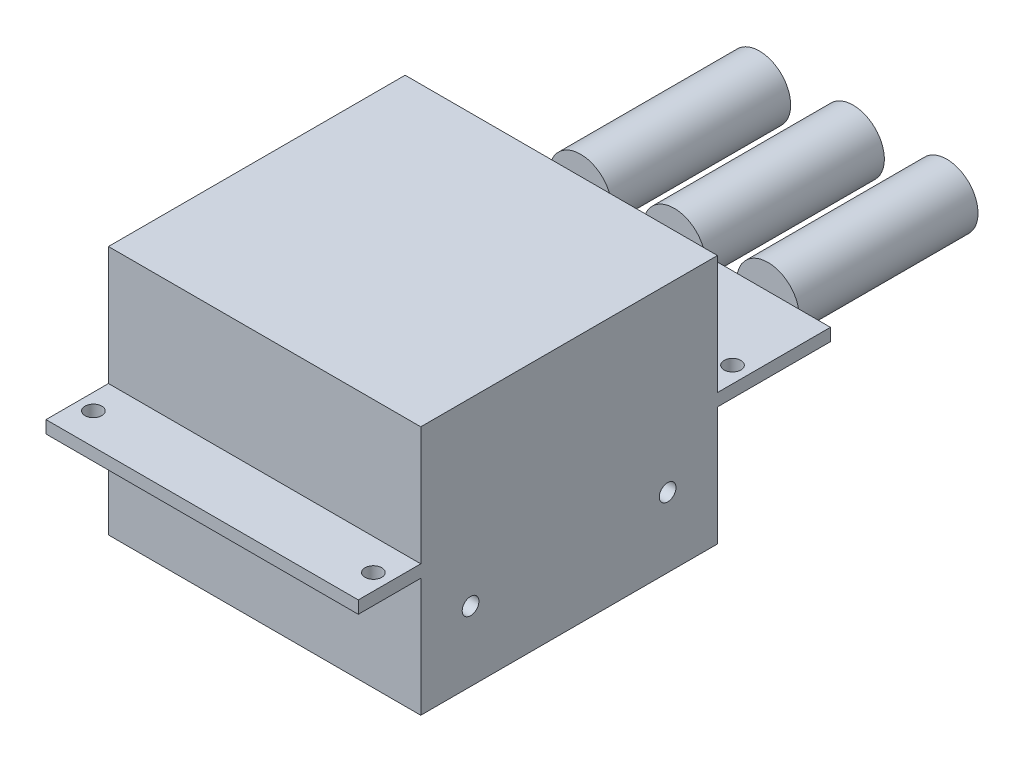
SolidWorks part; units mm, degrees
ref_plane "Front Plane" through (0, 0, 0) normal (0, 0, 1) x (1, 0, 0)
ref_plane "Top Plane" through (0, 0, 0) normal (0, 1, 0) x (1, 0, 0)
ref_plane "Right Plane" through (0, 0, 0) normal (1, 0, 0) x (0, 0, -1)
sketch "Sketch1" plane through (0, 0, 0) normal (0, 0, 1) x (1, 0, 0)
  line L1 (31.75, 25.4) -> (-31.75, 25.4)
  line L2 (31.75, 25.4) -> (31.75, -25.4)
  line L3 (31.75, -25.4) -> (-31.75, -25.4)
  line L4 (-31.75, 25.4) -> (-31.75, -25.4)
  line L5 (31.75, 25.4) -> (-31.75, -25.4) construction
  line L6 (31.75, -25.4) -> (-31.75, 25.4) construction
  point P0 (0, 0)
  dimension "D1" = 63.5
  dimension "D2" = 50.8
extrude "Boss-Extrude1" add sketch "Sketch1" against normal blind 96
sketch "Sketch2" plane through (0, 0, -96) normal (0, 0, -1) x (-1, 0, 0)
  line L1 (-12.7, 0) -> (-6.35, 0) construction
  line L2 (6.35, 0) -> (12.7, 0) construction
  circle A0 centre (0, 0) radius 6.35
  circle A1 centre (-19.05, 0) radius 6.35
  circle A2 centre (19.05, 0) radius 6.35
  dimension "D1" = 12.7
  dimension "D3" = 6.35
extrude "Boss-Extrude5" add sketch "Sketch2" along normal blind 36.36
sketch "Sketch3" plane through (31.75, 0, 0) normal (1, 0, 0) x (0, 0, -1)
  line L5 (0, -25.4) -> (12.7, -25.4)
  line L6 (0, -25.4) -> (0, -1.27)
  line L7 (0, -1.27) -> (12.7, -1.27)
  line L8 (12.7, -25.4) -> (12.7, -1.27)
  line L9 (96, -25.4) -> (73.025, -25.4)
  line L10 (96, -25.4) -> (96, -1.27)
  line L11 (96, -1.27) -> (73.025, -1.27)
  line L12 (73.025, -25.4) -> (73.025, -1.27)
  dimension "D1" = 1.27
  dimension "D2" = 12.7
  dimension "D3" = 60.325
extrude "Cut-Extrude1" cut sketch "Sketch3" against normal through all
ref_plane "Plane1" through (0, 0, 0) normal (0, 1, 0) x (1, 0, 0)
mirror "Mirror1" about plane through (0, 0, 0) normal (0, 1, 0) of "Cut-Extrude1"
sketch "Sketch4" plane through (0, 1.27, 0) normal (0, 1, 0) x (1, 0, 0)
  line L0 (-31.75, 73.025) -> (31.75, 73.025) construction
  line L1 (-31.75, 96) -> (-31.75, 73.025) construction
  circle A0 centre (-28.4625, 79.375) radius 1.7
  dimension "D1" = 3.4
  dimension "D3" = 1.5875
  dimension "D2" = 6.35
extrude "Cut-Extrude2" cut sketch "Sketch4" against normal blind 2.54
ref_plane "Plane8" through (0, 0, 0) normal (1, 0, 0) x (0, 0, -1)
ref_plane "Plane9" through (0, 0, -42.8625) normal (0, 0, -1) x (-1, 0, 0)
mirror "Mirror2" about plane through (0, 0, 0) normal (1, 0, 0) of "Cut-Extrude2"
mirror "Mirror3" about plane through (0, 0, -42.8625) normal (0, 0, -1) of "Mirror2", "Cut-Extrude2"
sketch "Sketch5" plane through (31.75, 0, 0) normal (1, 0, 0) x (0, 0, -1)
  line L0 (73.025, -25.4) -> (12.7, -25.4) construction
  line L1 (12.7, -25.4) -> (12.7, -1.27) construction
  circle A0 centre (22.8269, -11.225) radius 1.7
  dimension "D1" = 3.4
  dimension "D2" = 15.875
  dimension "D3" = 11.8269
extrude "Cut-Extrude3" cut sketch "Sketch5" against normal through all
mirror "Mirror4" about plane through (0, 0, -42.8625) normal (0, 0, -1) of "Cut-Extrude3"
